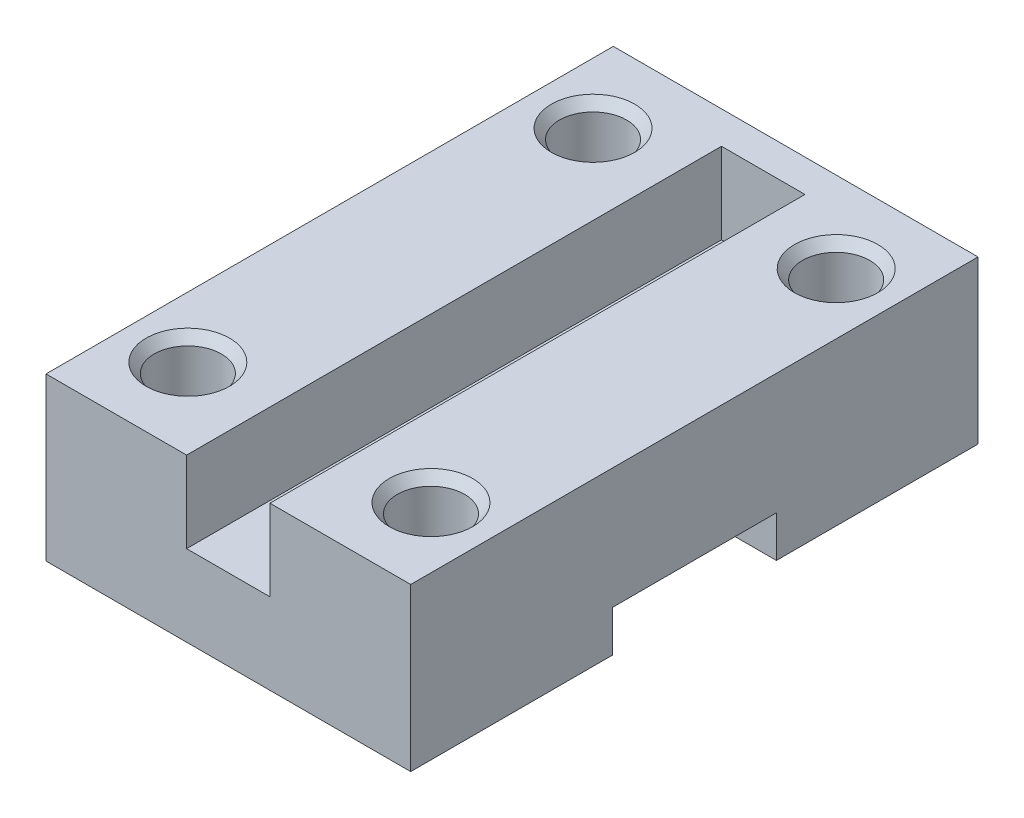
SolidWorks part; units mm, degrees
ref_plane "Спереди" through (0, 0, 0) normal (0, 0, 1) x (1, 0, 0)
ref_plane "Сверху" through (0, 0, 0) normal (0, 1, 0) x (1, 0, 0)
ref_plane "Справа" through (0, 0, 0) normal (1, 0, 0) x (0, 0, -1)
sketch "Sketch1" plane through (0, 0, 0) normal (0, 1, 0) x (1, 0, 0)
  line L1 (22.5, -35) -> (-22.5, -35)
  line L2 (22.5, -35) -> (22.5, 35)
  line L3 (22.5, 35) -> (-22.5, 35)
  line L4 (-22.5, -35) -> (-22.5, 35)
  line L5 (22.5, -35) -> (-22.5, 35) construction
  line L6 (22.5, 35) -> (-22.5, -35) construction
  point P0 (0, 0)
  dimension "D1" = 45
  dimension "D2" = 70
extrude "Boss-Extrude1" add sketch "Sketch1" along normal blind 10
sketch "Sketch2" plane through (22.5, 0, 0) normal (1, 0, 0) x (0, 0, -1)
  line L0 (0, 0) -> (0, 10) construction
  line L1 (-35, 0) -> (35, 0) construction
  line L2 (-35, 10) -> (35, 10) construction
  line L4 (10.125, 5.1) -> (-10.125, 5.1)
  line L5 (10.125, 5.1) -> (10.125, 0)
  line L6 (10.125, 0) -> (-10.125, 0)
  line L7 (-10.125, 5.1) -> (-10.125, 0)
  line L8 (10.125, 5.1) -> (-10.125, 0) construction
  line L9 (10.125, 0) -> (-10.125, 5.1) construction
  point P6 (0, 2.55)
  dimension "D1" = 20.25
  dimension "D2" = 5.1
extrude "Cut-Extrude1" cut sketch "Sketch2" against normal through all and the other way through all
sketch "Sketch3" plane through (0, 0, 0) normal (0, -1, 0) x (1, 0, 0)
  line L0 (15, -25) -> (15, 25) construction
  line L1 (-15, 25) -> (-15, -25) construction
  line L2 (-15, -25) -> (15, 25) construction
  line L3 (-22.5, -25) -> (22.5, -25) construction
  line L4 (-22.5, -35) -> (-22.5, -10.125) construction
  line L5 (22.5, -10.125) -> (22.5, -35) construction
  line L6 (-22.5, 25) -> (22.5, 25) construction
  line L7 (-22.5, 10.125) -> (-22.5, 35) construction
  line L8 (22.5, 35) -> (22.5, 10.125) construction
  line L9 (-15, 25) -> (15, -25) construction
  circle A0 centre (15, 25) radius 4.15
  circle A1 centre (15, -25) radius 4.15
  circle A2 centre (-15, -25) radius 4.15
  circle A3 centre (-15, 25) radius 4.15
  point P4 (0, 0)
  dimension "D1" = 8.3
  dimension "D2" = 30
  dimension "D3" = 50
extrude "Cut-Extrude2" cut sketch "Sketch3" against normal through all
sketch "Sketch5" plane through (0, 10, 0) normal (0, 1, 0) x (1, 0, 0)
  line L0 (5.15, 35) -> (-5.15, -35) construction
  line L1 (-5.15, -35) -> (-22.5, -35)
  line L2 (-5.15, -35) -> (-5.15, 35) construction
  line L3 (-5.15, 35) -> (-22.5, 35) construction
  line L4 (-22.5, -35) -> (-22.5, 35)
  line L5 (-5.15, -35) -> (-22.5, 35) construction
  line L6 (-5.15, 35) -> (-22.5, -35) construction
  line L7 (5.15, -35) -> (22.5, -35)
  line L8 (5.15, -35) -> (5.15, 35) construction
  line L9 (5.15, 35) -> (22.5, 35) construction
  line L10 (22.5, -35) -> (22.5, 35)
  line L11 (5.15, -35) -> (22.5, 35) construction
  line L12 (5.15, 35) -> (22.5, -35) construction
  line L13 (5.15, -35) -> (-5.15, 35) construction
  line L14 (-5.15, -35) -> (-5.15, 31)
  line L15 (-5.15, 31) -> (5.15, 31)
  line L16 (5.15, 31) -> (5.1302, -34.9493)
  line L17 (5.15, -35) -> (5.1302, -34.9493)
  line L18 (-22.5, 35) -> (22.5, 35)
  circle A0 centre (-15, 25) radius 4.15
  circle A1 centre (15, 25) radius 4.15
  circle A2 centre (15, -25) radius 4.15
  circle A3 centre (-15, -25) radius 4.15
  point P0 (-13.825, 0)
  point P6 (13.825, 0)
  point P12 (0, 0)
  dimension "D1" = 10.3
  dimension "D2" = 4
extrude "Boss-Extrude2" add sketch "Sketch5" along normal blind 10
chamfer "Chamfer1" distance 1 angle 50 4 edges at (15, 20, 29.15) (-15, 20, 29.15) (-15, 20, -20.85) (15, 20, -20.85)
